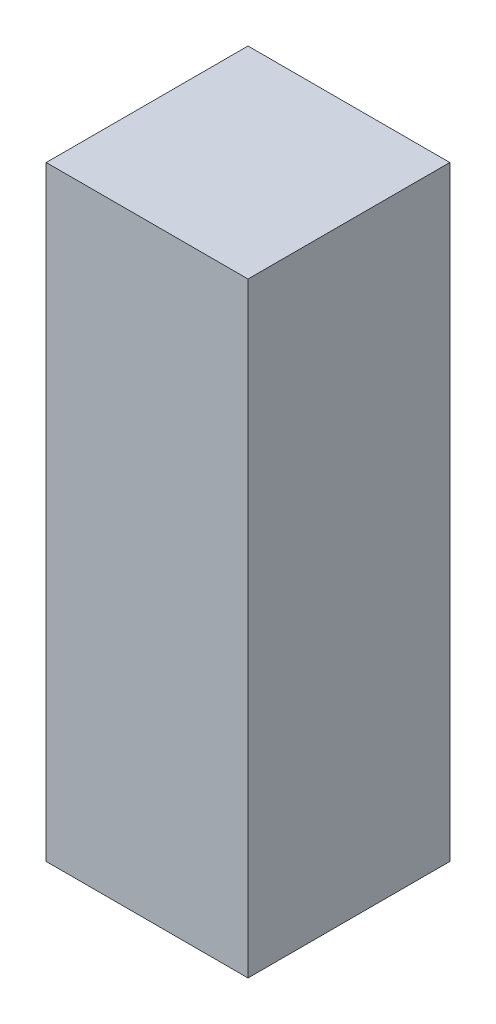
SolidWorks part; units mm, degrees
ref_plane "Front Plane" through (0, 0, 0) normal (0, 0, 1) x (1, 0, 0)
ref_plane "Top Plane" through (0, 0, 0) normal (0, 1, 0) x (1, 0, 0)
ref_plane "Right Plane" through (0, 0, 0) normal (1, 0, 0) x (0, 0, -1)
sketch "Model" plane through (0, 0, 0) normal (0, 0, 1) x (1, 0, 0)
  line L0 (36.9332, 7.0448) -> (30.9332, 7.0448)
  line L1 (36.9332, 25.0448) -> (30.9332, 25.0448)
  line L2 (30.9332, 25.0448) -> (30.9332, 7.0448)
  line L3 (36.9332, 25.0448) -> (36.9332, 7.0448)
extrude "Boss-Extrude1" add sketch "Model" along normal blind 6 contours L2 L0 L3 L1
